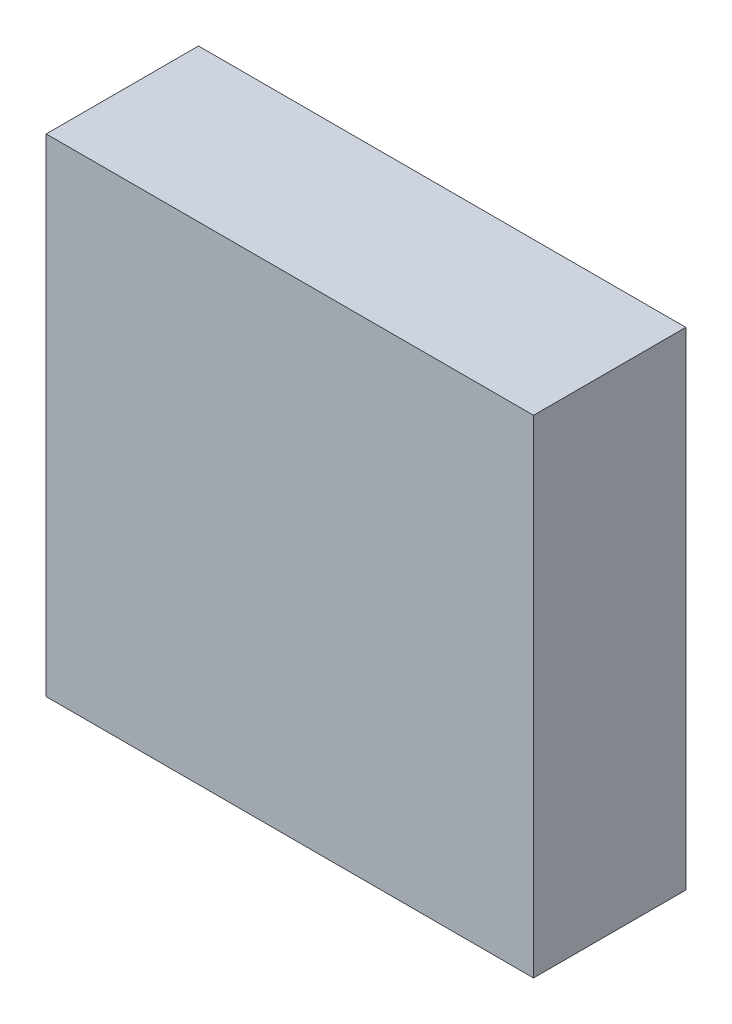
SolidWorks part; units mm, degrees
ref_plane "Front Plane" through (0, 0, 0) normal (0, 0, 1) x (1, 0, 0)
ref_plane "Top Plane" through (0, 0, 0) normal (0, 1, 0) x (1, 0, 0)
ref_plane "Right Plane" through (0, 0, 0) normal (1, 0, 0) x (0, 0, -1)
sketch "Sketch1" plane through (0, 0, 0) normal (0, 0, 1) x (1, 0, 0)
  line L1 (-34.6273, 47.6368) -> (45.3727, 47.6368)
  line L2 (-34.6273, 47.6368) -> (-34.6273, -32.3632)
  line L3 (-34.6273, -32.3632) -> (45.3727, -32.3632)
  line L4 (45.3727, 47.6368) -> (45.3727, -32.3632)
  dimension "D1" = 80
  dimension "D2" = 80
extrude "Boss-Extrude1" add sketch "Sketch1" along normal blind 25
